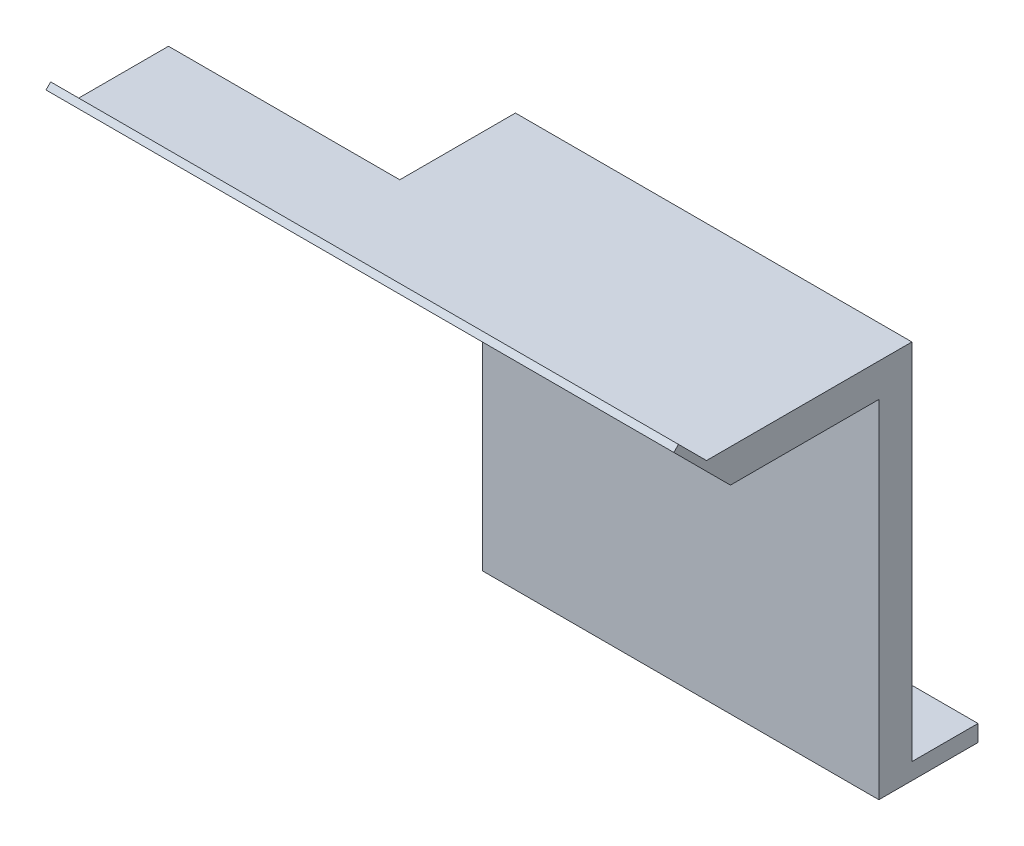
SolidWorks part; units mm, degrees
ref_plane "Front Plane" through (0, 0, 0) normal (0, 0, 1) x (1, 0, 0)
ref_plane "Top Plane" through (0, 0, 0) normal (0, 1, 0) x (1, 0, 0)
ref_plane "Right Plane" through (0, 0, 0) normal (1, 0, 0) x (0, 0, -1)
sketch "Sketch1" plane through (0, 0, 0) normal (0, 1, 0) x (1, 0, 0)
  line L1 (-6.9439, 31.9784) -> (145.4561, 31.9784)
  line L2 (-6.9439, 31.9784) -> (-6.9439, -6.1216)
  line L3 (-6.9439, -6.1216) -> (145.4561, -6.1216)
  line L4 (145.4561, 31.9784) -> (145.4561, -6.1216)
  dimension "D1" = 152.4
  dimension "D2" = 38.1
extrude "Boss-Extrude1" add sketch "Sketch1" along normal blind 6.35
sketch "Sketch2" plane through (0, 6.35, 0) normal (0, 1, 0) x (1, 0, 0)
  line L0 (-6.9439, 31.9784) -> (-6.9439, -6.1216) construction
  line L1 (145.4561, 31.9784) -> (-6.9439, 31.9784) construction
  circle A0 centre (-0.5939, 12.9284) radius 3.175
  circle A1 centre (24.8061, 12.9284) radius 3.175
  circle A2 centre (50.2061, 12.9284) radius 3.175
  circle A3 centre (75.6061, 12.9284) radius 3.175
  circle A4 centre (101.0061, 12.9284) radius 3.175
  circle A5 centre (126.4061, 12.9284) radius 3.175
  dimension "D1" = 6.35
  dimension "D3" = 6.35
  dimension "D4" = 19.05
  dimension "D2" = 6
extrude "Cut-Extrude1" cut sketch "Sketch2" against normal through all
sketch "Sketch3" plane through (0, 6.35, 0) normal (0, 1, 0) x (1, 0, 0)
  line L1 (-6.9439, 6.5784) -> (145.4561, 6.5784)
  line L2 (-6.9439, 6.5784) -> (-6.9439, -6.1216)
  line L3 (-6.9439, -6.1216) -> (145.4561, -6.1216)
  line L4 (145.4561, 6.5784) -> (145.4561, -6.1216)
  line L5 (-6.9439, 31.9784) -> (-6.9439, -6.1216) construction
  line L6 (145.4561, -6.1216) -> (145.4561, 31.9784) construction
  line L7 (-6.9439, -6.1216) -> (145.4561, -6.1216) construction
  dimension "D1" = 12.7
extrude "Boss-Extrude2" add sketch "Sketch3" along normal blind 139.7
sketch "Sketch4" plane through (-6.9439, 0, 0) normal (-1, 0, 0) x (0, 0, 1)
  line L1 (-6.5784, 146.05) -> (75.9716, 146.05)
  line L2 (-6.5784, 146.05) -> (-6.5784, 133.2565)
  line L3 (-6.5784, 133.2565) -> (75.9716, 133.2565)
  line L4 (75.9716, 146.05) -> (75.9716, 133.2565)
  line L6 (-6.5784, 146.05) -> (6.1216, 146.05) construction
  line L7 (-6.5784, 146.05) -> (-6.5784, 6.35) construction
  dimension "D1" = 12.7935
  dimension "D2" = 82.55
extrude "Boss-Extrude3" add sketch "Sketch4" against normal blind 152.4 and the other way blind 88.9
sketch "Sketch5" plane through (0, 146.05, 0) normal (0, 1, 0) x (1, 0, 0)
  line L0 (145.4561, 6.5784) -> (-95.8439, 6.5784) construction
  line L1 (-6.9439, -37.8716) -> (-95.8439, -37.8716)
  line L2 (-6.9439, -37.8716) -> (-6.9439, 6.5784)
  line L3 (-6.9439, 6.5784) -> (-95.8439, 6.5784)
  line L4 (-95.8439, -37.8716) -> (-95.8439, 6.5784)
  line L5 (-95.8439, -75.9716) -> (-95.8439, 6.5784) construction
  dimension "D1" = 88.9
  dimension "D2" = 44.45
extrude "Cut-Extrude2" cut sketch "Sketch5" against normal blind 152.4
sketch "Sketch6" plane through (-95.8439, 0, 0) normal (-1, 0, 0) x (0, 0, 1)
  line L0 (75.9716, 146.05) -> (63.1781, 133.2565)
  line L1 (63.1781, 133.2565) -> (75.9716, 133.2565)
  line L2 (75.9716, 133.2565) -> (75.9716, 146.05)
  line L3 (37.8716, 133.2565) -> (75.9716, 133.2565) construction
extrude "Cut-Extrude3" cut sketch "Sketch6" against normal through all
sketch "Sketch7" plane through (-95.8439, 0, 0) normal (-1, 0, 0) x (0, 0, 1)
  line L0 (75.9716, 146.05) -> (63.1781, 133.2565) construction
  line L1 (84.9518, 155.0303) -> (83.1558, 156.8263)
  line L2 (84.9518, 155.0303) -> (66.9913, 137.0697)
  line L3 (66.9913, 137.0697) -> (65.1953, 138.8658)
  line L4 (83.1558, 156.8263) -> (65.1953, 138.8658)
  point P6 (75.9716, 146.05)
  dimension "D1" = 25.4
  dimension "D2" = 2.54
extrude "Boss-Extrude4" add sketch "Sketch7" against normal through all
